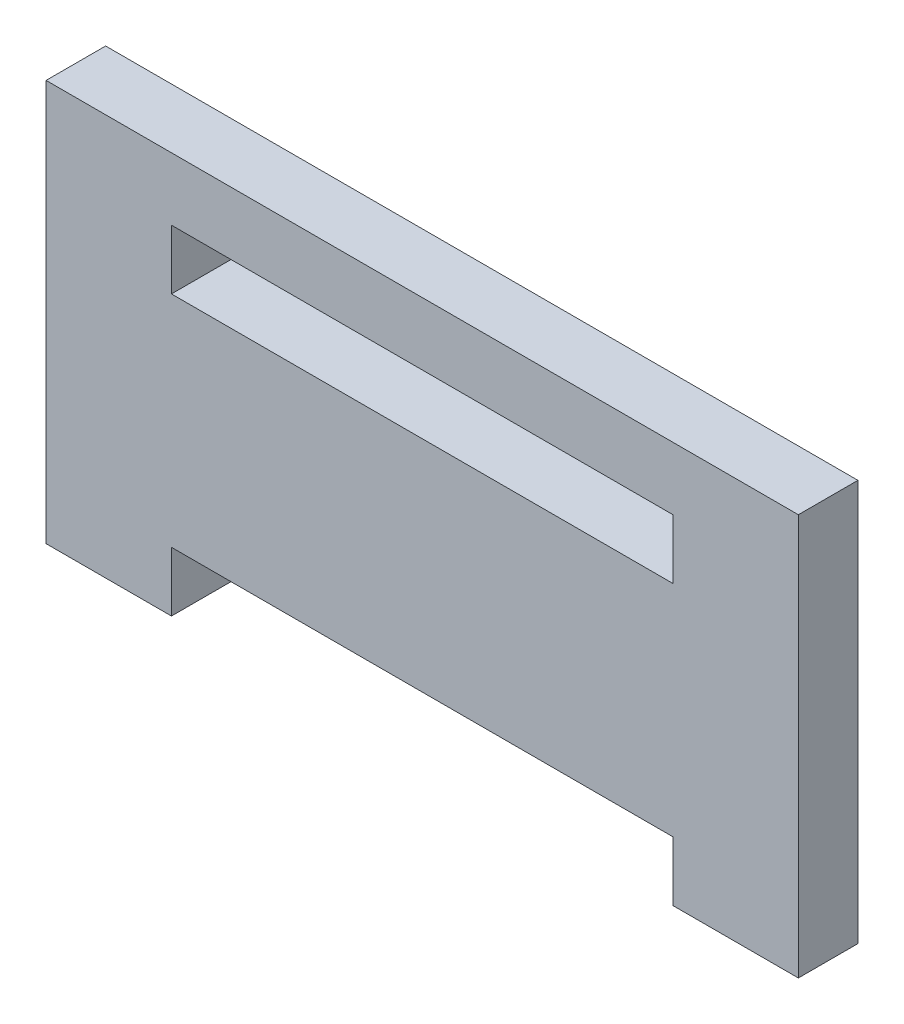
SolidWorks part; units mm, degrees
material "Pine"
ref_plane "Front Plane" through (0, 0, 0) normal (0, 0, 1) x (1, 0, 0)
ref_plane "Top Plane" through (0, 0, 0) normal (0, 1, 0) x (1, 0, 0)
ref_plane "Right Plane" through (0, 0, 0) normal (1, 0, 0) x (0, 0, -1)
sketch "Sketch1" plane through (0, 0, 0) normal (0, 0, 1) x (1, 0, 0)
  line L0 (0, 13.5) -> (60, 13.5) construction
  line L1 (0, 0) -> (10, 0)
  line L2 (0, 0) -> (0, 27)
  line L3 (0, 27) -> (10, 27)
  line L4 (60, 0) -> (60, 27)
  line L6 (10, 0) -> (10, 4.75)
  line L7 (10, 4.75) -> (50, 4.75)
  line L8 (50, 0) -> (50, 4.75)
  line L9 (10, 22.25) -> (50, 22.25)
  line L10 (50, 27) -> (50, 22.25)
  line L12 (10, 27) -> (10, 22.25)
  line L13 (50, 27) -> (60, 27)
  line L14 (50, 0) -> (60, 0)
  dimension "D1" = 27
  dimension "D2" = 60
  dimension "D3" = 10
  dimension "D4" = 10
  dimension "D5" = 4.75
extrude "Boss-Extrude1" add sketch "Sketch1" along normal blind 4.75
sketch "Sketch2" plane through (0, 27, 0) normal (0, 1, 0) x (1, 0, 0)
  line L1 (0, 0) -> (60, 0)
  line L2 (0, 0) -> (0, -4.75)
  line L3 (0, -4.75) -> (60, -4.75)
  line L4 (60, 0) -> (60, -4.75)
extrude "Boss-Extrude2" add sketch "Sketch2" along normal blind 5
